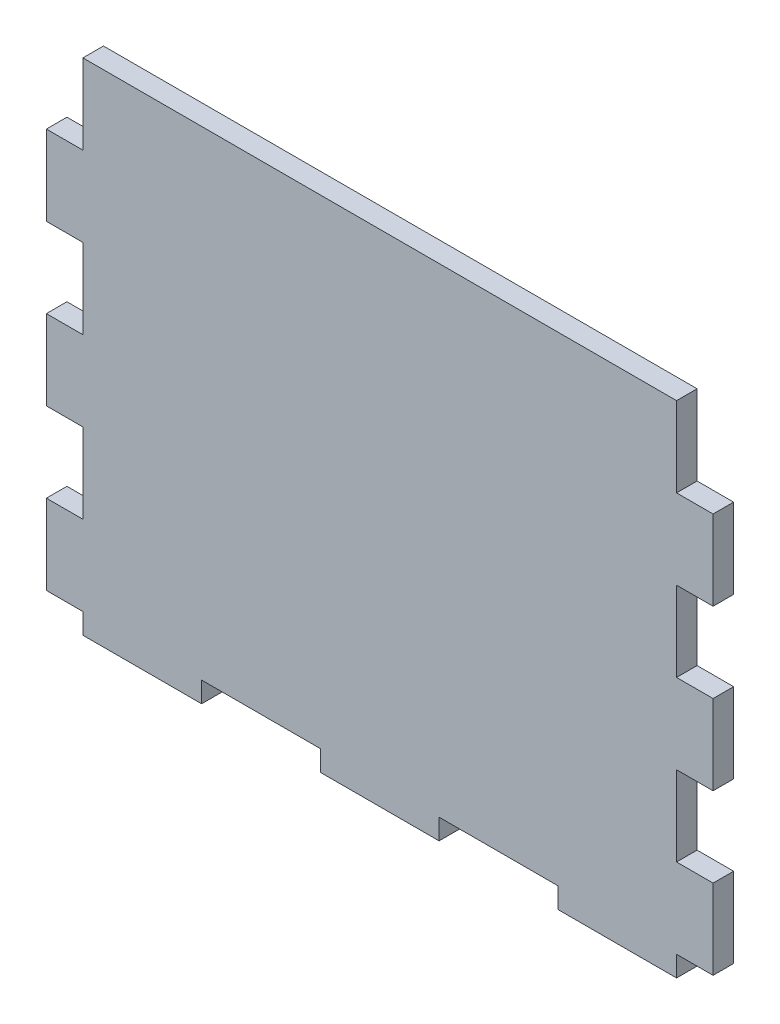
SolidWorks part; units mm, degrees
ref_plane "Front Plane" through (0, 0, 0) normal (0, 0, 1) x (1, 0, 0)
ref_plane "Top Plane" through (0, 0, 0) normal (0, 1, 0) x (1, 0, 0)
ref_plane "Right Plane" through (0, 0, 0) normal (1, 0, 0) x (0, 0, -1)
sketch "Sketch1" plane through (0, 0, 0) normal (0, 0, 1) x (1, 0, 0)
  line L1 (0, 0) -> (65, 0)
  line L2 (0, 0) -> (0, 70)
  line L3 (0, 70) -> (65, 70)
  line L4 (65, 0) -> (65, 70)
  dimension "D1" = 65
  dimension "D2" = 70
extrude "Boss-Extrude1" add sketch "Sketch1" along normal blind 2.25
sketch "Sketch2" plane through (0, 0, 2.25) normal (0, 0, 1) x (1, 0, 0)
  line L0 (-4, 8.75) -> (-4, 17.5) construction
  line L1 (0, 0) -> (-4, 0)
  line L2 (0, 0) -> (0, 8.75)
  line L3 (0, 8.75) -> (-4, 8.75)
  line L4 (-4, 0) -> (-4, 8.75)
  line L5 (0, 17.5) -> (-4, 17.5)
  line L6 (0, 17.5) -> (0, 26.25)
  line L7 (0, 26.25) -> (-4, 26.25)
  line L8 (-4, 17.5) -> (-4, 26.25)
  line L9 (-4, 26.25) -> (-4, 35) construction
  line L10 (0, 35) -> (-4, 35)
  line L11 (0, 35) -> (0, 43.75)
  line L12 (0, 43.75) -> (-4, 43.75)
  line L13 (-4, 35) -> (-4, 43.75)
  line L14 (-4, 43.75) -> (-4, 52.5) construction
  line L15 (0, 52.5) -> (-4, 52.5)
  line L16 (0, 52.5) -> (0, 61.25)
  line L17 (0, 61.25) -> (-4, 61.25)
  line L18 (-4, 52.5) -> (-4, 61.25)
  line L19 (-4, 61.25) -> (-4, 70) construction
  line L20 (65, 70) -> (0, 70) construction
  line L21 (32.5, 0) -> (32.5, 70) construction
  line L22 (0, 0) -> (65, 0) construction
  line L23 (69, 61.25) -> (69, 70) construction
  line L24 (69, 43.75) -> (69, 52.5) construction
  line L25 (69, 26.25) -> (69, 35) construction
  line L26 (69, 8.75) -> (69, 17.5) construction
  line L27 (69, 52.5) -> (69, 61.25)
  line L28 (65, 61.25) -> (69, 61.25)
  line L29 (65, 52.5) -> (65, 61.25)
  line L30 (65, 52.5) -> (69, 52.5)
  line L31 (69, 35) -> (69, 43.75)
  line L32 (65, 43.75) -> (69, 43.75)
  line L33 (65, 35) -> (65, 43.75)
  line L34 (65, 35) -> (69, 35)
  line L35 (69, 17.5) -> (69, 26.25)
  line L36 (65, 26.25) -> (69, 26.25)
  line L37 (65, 17.5) -> (65, 26.25)
  line L38 (65, 17.5) -> (69, 17.5)
  line L39 (69, 0) -> (69, 8.75)
  line L40 (65, 8.75) -> (69, 8.75)
  line L41 (65, 0) -> (65, 8.75)
  line L42 (65, 0) -> (69, 0)
  line L43 (13, -2.25) -> (26, -2.25) construction
  line L44 (0, 0) -> (13, 0)
  line L45 (0, 0) -> (0, -2.25)
  line L46 (0, -2.25) -> (13, -2.25)
  line L47 (13, 0) -> (13, -2.25)
  line L48 (26, 0) -> (26, -2.25)
  line L49 (26, -2.25) -> (39, -2.25)
  line L50 (39, 0) -> (39, -2.25)
  line L51 (39, -2.25) -> (52, -2.25) construction
  line L52 (26, 0) -> (39, 0)
  line L53 (52, 0) -> (52, -2.25)
  line L54 (52, -2.25) -> (65, -2.25)
  line L55 (65, 0) -> (65, -2.25)
  line L56 (65, -2.25) -> (78, -2.25) construction
  line L57 (52, 0) -> (65, 0)
  line M26 (0, 70) -> (0, 0)
  line M27 (0, 0) -> (65, 0)
  line M28 (65, 0) -> (65, 70)
  dimension "D2" = 4
  dimension "D4" = 2.25
  dimension "D1" = 4
  dimension "D3" = 3
extrude "Boss-Extrude2" add sketch "Sketch2" against normal up to surface (2.25 mm away) contours L34 L31 L32 M28 | L38 L35 L36 M28 | L42 L39 L40 M28 | L47 L45 L46 M27 | L4 L1 L3 M26 | L8 L5 L7 M26 | L18 L15 L17 M26 | L29 L28 L27 L30 | L57 L53 L54 L55 | L49 L50 L52 L48 | L13 L12 L11 L10 up to face at (32.5, 35, 0)
sketch "Sketch3" plane through (0, 0, 0) normal (0, 0, -1) x (-1, 0, 0)
  line L0 (-65, 70) -> (0, 70) construction
  line L1 (-69, 70) -> (4, 70)
  line L2 (-69, 70) -> (-69, 52.5)
  line L3 (-69, 52.5) -> (4, 52.5)
  line L4 (4, 70) -> (4, 52.5)
  line L5 (4, 17.5) -> (4, 26.25) construction
  line L6 (-69, 35) -> (-69, 43.75) construction
  line L7 (0, 52.5) -> (4, 52.5) construction
  line L8 (4, 52.5) -> (4, 61.25) construction
extrude "Cut-Extrude1" cut sketch "Sketch3" against normal through all
equation "\"D1@Boss-Extrude1\"=\"thick\" + \"veneer_thickness\""
equation "\"D2@Sketch2\"=\"thick\"*2 + \"veneer_thickness\""
equation "\"D4@Sketch2\"=\"thick\" + \"veneer_thickness\""
equation "\"veneer_thickness\"= 0.5mm"
equation "\"thick\"= 1.75mm"
